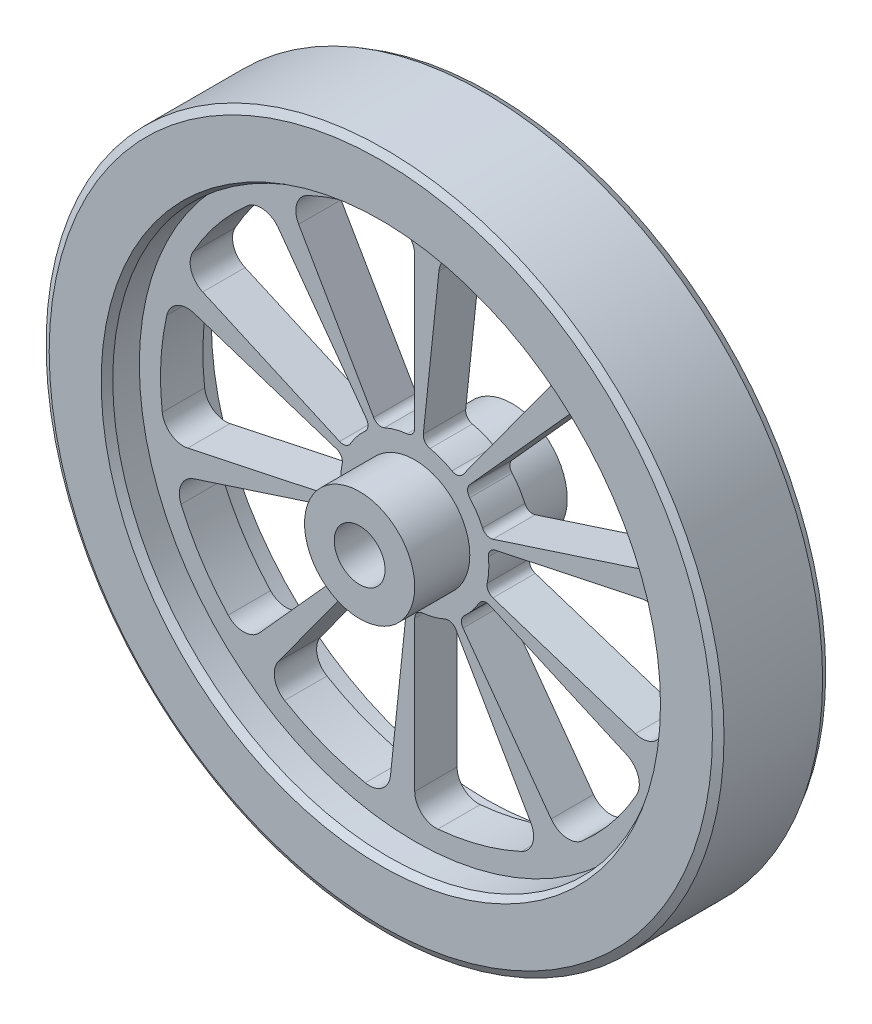
SolidWorks part; units mm, degrees
ref_plane "Front Plane" through (0, 0, 0) normal (0, 0, 1) x (1, 0, 0)
ref_plane "Top Plane" through (0, 0, 0) normal (0, 1, 0) x (1, 0, 0)
ref_plane "Right Plane" through (0, 0, 0) normal (1, 0, 0) x (0, 0, -1)
sketch "Sketch1" plane through (0, 0, 0) normal (0, 0, 1) x (1, 0, 0)
  circle A0 centre (0, 0) radius 80
  circle A1 centre (0, 0) radius 6
  dimension "D1" = 160
  dimension "D2" = 12
extrude "Boss-Extrude1" add sketch "Sketch1" along normal mid plane 26
sketch "Sketch2" plane through (0, 0, 13) normal (0, 0, 1) x (1, 0, 0)
  circle A0 centre (0, 0) radius 65
  dimension "D1" = 130
extrude "Cut-Extrude1" cut sketch "Sketch2" against normal blind 8
mirror "Mirror1" about plane through (0, 0, 0) normal (0, 0, 1) of "Cut-Extrude1"
sketch "Sketch3" plane through (0, 0, 0) normal (0, 0, 1) x (1, 0, 0)
  circle A2 centre (0, 0) radius 13
  circle A3 centre (0, 0) radius 6 construction
  circle A4 centre (0, 0) radius 6
  dimension "D1" = 26
extrude "Boss-Extrude3" add sketch "Sketch3" along normal mid plane 36
chamfer "Chamfer1" distance 1 angle 60 4 edges at (80, 0, -13) (65, 0, -13) (80, 0, 13) (65, 0, 13)
sketch "Sketch4" plane through (0, 0, 5) normal (0, 0, 1) x (1, 0, 0)
  line L0 (0, 17.5) -> (0, 60) construction
  line L1 (-8.75, 15.1554) -> (-27.3861, 47.4342) construction
  line L2 (0, 54.7723) -> (0, 19.3972)
  line L3 (-9.6986, 16.7984) -> (-27.3861, 47.4342)
  arc A0 (-1.7949, 17.4077) -> (-7.1495, 15.973) centre (0, 0) ccw
  arc A1 (-5.4545, 59.7516) -> (-25.152, 54.4736) centre (0, 0) ccw
  arc A2 (-5.4545, 59.7516) -> (0, 54.7723) centre (-5, 54.7723) cw
  arc A3 (-25.152, 54.4736) -> (-27.3861, 47.4342) centre (-23.056, 49.9342) ccw
  arc A4 (0, 19.3972) -> (-1.7949, 17.4077) centre (-2, 19.3972) cw
  circle A5 centre (0, 0) radius 65 construction
  arc A6 (-7.1495, 15.973) -> (-9.6986, 16.7984) centre (-7.9665, 17.7984) cw
  dimension "D1" = 120
  dimension "D2" = 35
  dimension "D4" = 5
  dimension "D5" = 2
  dimension "D3" = 30
extrude "Cut-Extrude2" cut sketch "Sketch4" against normal through all
pattern_circular "CirPattern1" count 10 over 360 about axis through (0, 0, 0) along (0, 0, 1) of "Cut-Extrude2"
